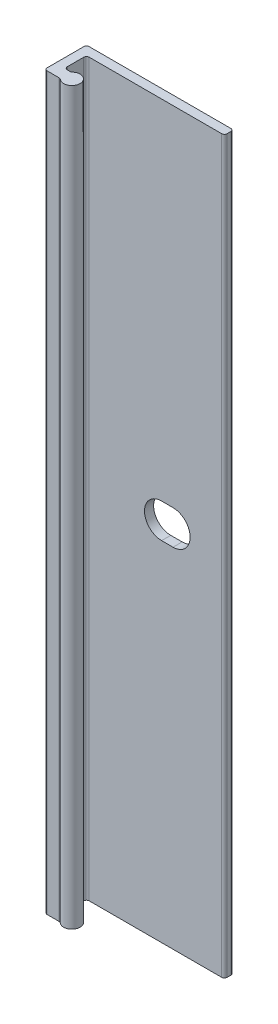
SolidWorks part; units mm, degrees
material "6463-T6"
ref_plane "Front Plane" through (0, 0, 0) normal (0, 0, 1) x (1, 0, 0)
ref_plane "Top Plane" through (0, 0, 0) normal (0, 1, 0) x (1, 0, 0)
ref_plane "Right Plane" through (0, 0, 0) normal (1, 0, 0) x (0, 0, -1)
sketch "Sketch2" plane through (0, 0, 0) normal (0, 1, 0) x (1, 0, 0)
  line L0 (0, -55) -> (0, 55) construction
  line L16 (0.381, 0) -> (20.066, 0)
  line L18 (20.447, -0.381) -> (20.447, -0.889)
  line L19 (20.066, -1.27) -> (1.651, -1.27)
  line L20 (1.27, -1.651) -> (1.27, -3.937)
  line L52 (0, -0.381) -> (0, -5.461)
  line L55 (0.381, -5.842) -> (2.04, -5.842)
  line L56 (1.651, -4.318) -> (2.04, -4.318)
  arc A11 (20.066, 0) -> (20.447, -0.381) centre (20.066, -0.381) cw
  arc A12 (20.447, -0.889) -> (20.066, -1.27) centre (20.066, -0.889) cw
  arc A19 (1.651, -1.27) -> (1.27, -1.651) centre (1.651, -1.651) ccw
  arc A21 (2.292, -5.9372) -> (2.292, -4.2227) centre (3.048, -5.08) ccw
  arc A22 (1.27, -3.937) -> (1.651, -4.318) centre (1.651, -3.937) ccw
  arc A24 (2.04, -5.842) -> (2.292, -5.9372) centre (2.04, -6.223) cw
  arc A25 (2.292, -4.2227) -> (2.04, -4.318) centre (2.04, -3.937) cw
  arc A26 (0.381, -5.842) -> (0, -5.461) centre (0.381, -5.461) cw
  arc A27 (0.381, 0) -> (0, -0.381) centre (0.381, -0.381) ccw
  point P7 (0, -5.842)
  point P16 (20.447, 0)
  point P19 (20.447, -1.27)
  point P22 (1.27, -1.27)
  point P30 (1.27, -4.318)
  point P36 (2.1961, -5.842)
  point P39 (2.1961, -4.318)
  point P43 (0, 0)
  dimension "D1" = 20.447
  dimension "D7" = 0.381
  dimension "D6" = 5.08
  dimension "D10" = 0.389
  dimension "D9" = 1.143
  dimension "D4" = 0.381
  dimension "D2" = 1.27
  dimension "D3" = 1.27
  dimension "D5" = 5.842
  dimension "D8" = 3.048
extrude "Boss-Extrude1" add sketch "Sketch2" along normal mid plane 101.6
sketch "Sketch7" plane through (0, 0, 1.27) normal (0, 0, 1) x (1, 0, 0)
  line L0 (11.7158, 0) -> (13.3033, 0) construction
  line L1 (11.7158, 2.3812) -> (13.3033, 2.3813)
  line L2 (11.7158, -2.3813) -> (13.3033, -2.3813)
  line L3 (0, 0) -> (20.447, 0) construction
  line L4 (20.447, 50.8) -> (20.447, -50.8) construction
  arc A0 (11.7158, 2.3812) -> (11.7158, -2.3813) centre (11.7158, 0) ccw
  arc A1 (13.3033, -2.3813) -> (13.3033, 2.3813) centre (13.3033, 0) ccw
  point P3 (12.5095, 0)
  dimension "D1" = 4.7625
  dimension "D2" = 6.35
  dimension "D3" = 7.9375
extrude "Cut-Extrude1" cut sketch "Sketch7" against normal through all
